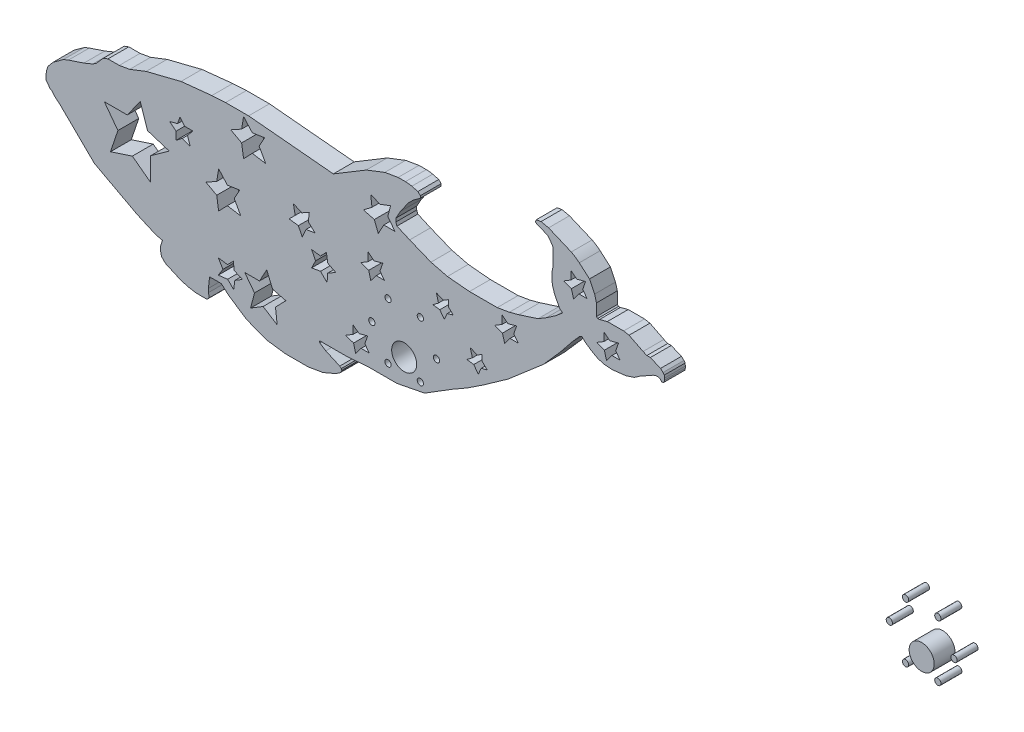
SolidWorks part; units mm, degrees
ref_plane "前视基准面" through (0, 0, 0) normal (0, 0, 1) x (1, 0, 0)
ref_plane "上视基准面" through (0, 0, 0) normal (0, 1, 0) x (1, 0, 0)
ref_plane "右视基准面" through (0, 0, 0) normal (1, 0, 0) x (0, 0, -1)
sketch "草图1" plane through (0, 0, 0) normal (0, 0, 1) x (1, 0, 0)
  line L0 (83.5762, -152.1775) -> (616.9095, -152.1775) construction
  line L5 (70.5984, -139.437) -> (603.9317, -139.437) construction
  line L6 (-33.4107, 54.8311) -> (-37.6598, 53.0815)
  line L7 (-37.6598, 53.0815) -> (-42.0588, 51.6318)
  line L8 (-42.0588, 51.6318) -> (-45.0467, 50.6472)
  line L9 (-45.0467, 50.6472) -> (-47.4328, 49.6647)
  line L10 (-47.4328, 49.6647) -> (-49.7572, 47.9826)
  line L11 (-49.7572, 47.9826) -> (-51.1926, 46.9439)
  line L12 (-51.1926, 46.9439) -> (-52.408, 46.0643)
  line L13 (-52.408, 46.0643) -> (-53.6631, 44.5741)
  line L14 (-53.6631, 44.5741) -> (-54.8675, 43.1441)
  line L15 (-54.8675, 43.1441) -> (-55.4833, 41.2781)
  line L20 (-55.8277, 37.0689) -> (-55.0465, 35.9894)
  line L21 (-55.0465, 35.9894) -> (-53.6631, 34.0778)
  line L22 (-53.6631, 34.0778) -> (-53.0356, 34.0778)
  line L23 (-53.0356, 34.0778) -> (-51.8003, 32.3709)
  line L24 (-51.8003, 32.3709) -> (-49.7572, 30.6501)
  line L25 (-49.7572, 30.6501) -> (-48.9668, 29.9844)
  line L26 (-48.9668, 29.9844) -> (-40.5644, 21.7347)
  line L27 (-40.5644, 21.7347) -> (-32.6032, 13.9182)
  line L28 (-32.6032, 13.9182) -> (-27.2854, 11.0838)
  line L29 (-27.2854, 11.0838) -> (-23.2682, 8.9427)
  line L30 (-23.2682, 8.9427) -> (-20.2984, 7.3598)
  line L31 (-20.2984, 7.3598) -> (-16.8647, 5.5296)
  line L32 (-16.8647, 5.5296) -> (-12.13, 3.0061)
  line L33 (-12.13, 3.0061) -> (-7.8019, 1.089)
  line L34 (-7.8019, 1.089) -> (-4.074, -0.5623)
  line L35 (-4.074, -0.5623) -> (-0.6643, -1.6353)
  line L36 (-0.6643, -1.6353) -> (0, -1.6353)
  line L37 (0, -1.6353) -> (-0.9026, -4.5034)
  line L38 (-0.9026, -4.5034) -> (-0.9026, -6.541)
  line L57 (22.4574, -6.541) -> (22.4574, -5.5222)
  line L58 (22.4574, -5.5222) -> (26.7724, -5.5222)
  line L59 (26.7724, -5.5222) -> (28.1702, -5.5222)
  line L60 (28.1702, -5.5222) -> (31.7282, -8.649)
  line L61 (31.7282, -8.649) -> (35.5739, -11.2197)
  line L62 (35.5739, -11.2197) -> (39.8011, -14.0455)
  line L63 (39.8011, -14.0455) -> (44.1213, -15.9591)
  line L64 (44.1213, -15.9591) -> (49.9981, -18.0843)
  line L65 (49.9981, -18.0843) -> (54.9833, -18.758)
  line L66 (54.9833, -18.758) -> (58.9433, -19.2932)
  line L67 (58.9433, -19.2932) -> (64.9003, -19.2932)
  line L68 (64.9003, -19.2932) -> (69.8738, -19.2932)
  line L69 (69.8738, -19.2932) -> (76.9587, -18.0843)
  line L70 (76.9587, -18.0843) -> (81.9059, -15.9591)
  line L71 (81.9059, -15.9591) -> (84.7973, -14.43)
  line L72 (84.7973, -14.43) -> (85.7047, -13.3974)
  line L73 (85.7047, -13.3974) -> (85.9813, -12.6326)
  line L74 (85.9813, -12.6326) -> (85.7274, -12.0415)
  line L75 (85.7274, -12.0415) -> (84.9774, -11.3825)
  line L76 (84.9774, -11.3825) -> (83.1426, -10.5697)
  line L77 (83.1426, -10.5697) -> (78.2926, -8.4214)
  line L78 (78.2926, -8.4214) -> (75.9827, -6.8773)
  line L79 (75.9827, -6.8773) -> (75.4796, -6.541)
  line L80 (75.4796, -6.541) -> (75.2607, -6.0316)
  line L81 (75.2607, -6.0316) -> (75.2607, -5.6862)
  line L82 (75.2607, -5.6862) -> (77.4695, -5.6862)
  line L83 (77.4695, -5.6862) -> (88.6645, -5.6862)
  line L84 (88.6645, -5.6862) -> (98.3767, -4.8754)
  line L87 (125.6251, -2.2946) -> (128.8782, -0.2757)
  line L88 (128.8782, -0.2757) -> (139.0992, 6.0678)
  line L89 (139.0992, 6.0678) -> (145.991, 10.0132)
  line L90 (145.991, 10.0132) -> (154.1306, 15.4027)
  line L91 (154.1306, 15.4027) -> (165.6842, 23.5709)
  line L92 (165.6842, 23.5709) -> (174.7548, 31.3817)
  line L93 (174.7548, 31.3817) -> (182.7359, 38.2543)
  line L94 (182.7359, 38.2543) -> (190.688, 47.3033)
  line L95 (190.688, 47.3033) -> (196.4524, 54.437)
  line L96 (196.4524, 54.437) -> (199.7963, 58.2421)
  line L97 (199.7963, 58.2421) -> (200.6278, 58.8201)
  line L98 (200.6278, 58.8201) -> (201.3219, 58.8201)
  line L99 (201.3219, 58.8201) -> (201.7237, 58.2421)
  line L100 (201.7237, 58.2421) -> (202.973, 57.1442)
  line L101 (202.973, 57.1442) -> (205.3877, 55.4732)
  line L102 (205.3877, 55.4732) -> (208.6354, 53.6139)
  line L103 (208.6354, 53.6139) -> (211.8335, 52.7462)
  line L104 (211.8335, 52.7462) -> (215.4778, 52.4239)
  line L105 (215.4778, 52.4239) -> (222.1425, 53.18)
  line L106 (222.1425, 53.18) -> (226.2551, 54.5436)
  line L107 (226.2551, 54.5436) -> (228.7947, 56.3087)
  line L108 (228.7947, 56.3087) -> (233.2216, 58.8201)
  line L109 (233.2216, 58.8201) -> (235.1797, 59.9309)
  line L110 (235.1797, 59.9309) -> (236.6838, 60.4296)
  line L111 (236.6838, 60.4296) -> (237.6413, 60.4296)
  line L112 (237.6413, 60.4296) -> (238.7462, 59.9309)
  line L113 (238.7462, 59.9309) -> (239.1322, 59.3755)
  line L114 (239.1322, 59.3755) -> (239.4779, 59.2195)
  line L115 (239.4779, 59.2195) -> (239.8353, 59.2195)
  line L116 (239.8353, 59.2195) -> (240.4593, 59.6532)
  line L117 (240.4593, 59.6532) -> (240.6282, 60.5924)
  line L118 (240.6282, 60.5924) -> (240.6282, 61.4324)
  line L119 (240.6282, 61.4324) -> (240.5437, 62.6546)
  line L120 (240.5437, 62.6546) -> (239.9752, 63.4725)
  line L121 (239.9752, 63.4725) -> (238.7462, 64.5403)
  line L122 (238.7462, 64.5403) -> (236.6838, 65.4133)
  line L123 (236.6838, 65.4133) -> (235.1797, 66.05)
  line L124 (235.1797, 66.05) -> (233.8657, 66.6062)
  line L125 (233.8657, 66.6062) -> (232.1914, 66.6062)
  line L126 (232.1914, 66.6062) -> (230.3774, 67.3741)
  line L127 (230.3774, 67.3741) -> (225.9144, 69.6248)
  line L128 (225.9144, 69.6248) -> (223.6572, 70.7632)
  line L129 (223.6572, 70.7632) -> (221.0484, 71.2325)
  line L130 (221.0484, 71.2325) -> (219.2218, 71.2325)
  line L131 (219.2218, 71.2325) -> (213.2492, 71.2325)
  line L132 (213.2492, 71.2325) -> (209.478, 70.194)
  line L133 (209.478, 70.194) -> (208.6354, 70.194)
  line L134 (208.6354, 70.194) -> (208.0377, 70.7133)
  line L135 (208.0377, 70.7133) -> (208.0377, 73.1258)
  line L136 (208.0377, 73.1258) -> (208.0377, 76.3796)
  line L137 (208.0377, 76.3796) -> (207.1546, 79.5865)
  line L138 (207.1546, 79.5865) -> (204.6981, 84.6475)
  line L139 (204.6981, 84.6475) -> (199.7963, 88.906)
  line L140 (195.939, 91.4741) -> (190.688, 93.6969)
  line L141 (190.688, 93.6969) -> (186.8388, 95.3263)
  line L142 (186.8388, 95.3263) -> (185.0851, 96.0686)
  line L143 (185.0851, 96.0686) -> (181.4705, 96.8481)
  line L144 (181.4705, 96.8481) -> (179.1749, 96.4584)
  line L145 (179.1749, 96.4584) -> (178.653, 95.2254)
  line L146 (178.653, 95.2254) -> (179.7411, 94.7648)
  line L147 (179.7411, 94.7648) -> (182.264, 93.6969)
  line L148 (182.264, 93.6969) -> (184.6819, 92.6734)
  line L149 (184.6819, 92.6734) -> (185.9619, 91.1644)
  line L150 (185.9619, 91.1644) -> (187.1532, 89.1995)
  line L151 (187.1532, 89.1995) -> (187.1532, 86.7554)
  line L152 (187.1532, 86.7554) -> (187.1532, 83.0174)
  line L153 (187.1532, 83.0174) -> (187.1532, 80.6692)
  line L154 (187.1532, 80.6692) -> (186.6424, 78.3005)
  line L155 (186.6424, 78.3005) -> (186.6424, 76.3796)
  line L156 (186.6424, 76.3796) -> (186.6424, 75.1921)
  line L157 (186.6424, 75.1921) -> (187.0459, 72.8151)
  line L158 (187.0459, 72.8151) -> (187.8822, 70.194)
  line L159 (187.8822, 70.194) -> (189.2793, 67.3741)
  line L160 (189.2793, 67.3741) -> (190.2507, 65.4133)
  line L161 (190.2507, 65.4133) -> (191.8011, 64.071)
  line L162 (191.8011, 64.071) -> (188.5807, 61.3393)
  line L163 (188.5807, 61.3393) -> (184.0423, 58.2421)
  line L164 (184.0423, 58.2421) -> (179.9948, 55.7882)
  line L165 (179.9948, 55.7882) -> (176.1321, 54.5558)
  line L166 (176.1321, 54.5558) -> (170.8442, 52.8687)
  line L167 (170.8442, 52.8687) -> (166.275, 51.6318)
  line L168 (166.275, 51.6318) -> (162.4428, 50.9811)
  line L169 (162.4428, 50.9811) -> (160.4758, 50.6472)
  line L170 (160.4758, 50.6472) -> (147.1514, 50.6472)
  line L171 (147.1514, 50.6472) -> (136.6018, 51.6318)
  line L172 (136.6018, 51.6318) -> (128.697, 53.6139)
  line L173 (128.697, 53.6139) -> (118.4882, 57.7541)
  line L174 (118.4882, 57.7541) -> (112.413, 60.4296)
  line L175 (112.413, 60.4296) -> (111.8604, 61.8521)
  line L176 (111.8604, 61.8521) -> (111.8604, 63.4725)
  line L177 (111.8604, 63.4725) -> (114.0757, 67.3741)
  line L178 (114.0757, 67.3741) -> (117.8675, 72.8151)
  line L179 (117.8675, 72.8151) -> (120.3102, 75.1921)
  line L180 (120.3102, 75.1921) -> (122.6457, 76.8963)
  line L181 (122.6457, 76.8963) -> (123.5926, 77.5873)
  line L182 (123.5926, 77.5873) -> (123.5926, 78.6479)
  line L183 (123.5926, 78.6479) -> (122.4473, 79.8248)
  line L184 (122.4473, 79.8248) -> (119.527, 80.5571)
  line L185 (116.4835, 80.9328) -> (112.968, 80.9328)
  line L186 (112.968, 80.9328) -> (106.5857, 79.8248)
  line L187 (106.5857, 79.8248) -> (97.718, 76.3796)
  line L188 (97.718, 76.3796) -> (91.8005, 72.8151)
  line L189 (91.8005, 72.8151) -> (86.9276, 69.8798)
  line L190 (86.9276, 69.8798) -> (83.1426, 67.5998)
  line L191 (83.1426, 67.5998) -> (81.9059, 66.8548)
  line L192 (81.9059, 66.8548) -> (61.7102, 68.7398)
  line L193 (61.7102, 68.7398) -> (49.496, 69.8798)
  line L194 (49.496, 69.8798) -> (41.2874, 70.6459)
  line L195 (41.2874, 70.6459) -> (35.0487, 70.6459)
  line L196 (35.0487, 70.6459) -> (30.2431, 70.6459)
  line L197 (30.2431, 70.6459) -> (23.667, 70.2629)
  line L198 (23.667, 70.2629) -> (8.9087, 68.7398)
  line L199 (8.9087, 68.7398) -> (-7.8019, 64.5403)
  line L200 (-7.8019, 64.5403) -> (-15.705, 61.4699)
  line L201 (-15.705, 61.4699) -> (-20.7029, 60.5924)
  line L202 (-20.7029, 60.5924) -> (-24.374, 60.5924)
  line L203 (-24.374, 60.5924) -> (-26.1248, 60.5924)
  line L204 (-26.1248, 60.5924) -> (-28.3735, 59.7188)
  line L205 (-28.3735, 59.7188) -> (-30.1347, 57.7541)
  line L206 (-30.1347, 57.7541) -> (-31.7347, 55.9692)
  line L207 (-31.7347, 55.9692) -> (-33.4107, 54.8311)
  line L208 (142.6379, -266.3219) -> (825.3045, -266.3219) construction
  line L209 (66.7963, 43.1441) -> (70.4146, 45.1685)
  line L210 (70.4146, 45.1685) -> (69.8738, 41.0482)
  line L211 (69.8738, 41.0482) -> (73.1335, 37.9737)
  line L212 (73.1335, 37.9737) -> (68.8251, 37.2626)
  line L213 (68.8251, 37.2626) -> (67.0264, 33.226)
  line L214 (67.0264, 33.226) -> (65.1231, 36.9943)
  line L215 (65.1231, 36.9943) -> (60.6892, 37.5763)
  line L216 (60.6892, 37.5763) -> (63.6172, 40.4835)
  line L217 (63.6172, 40.4835) -> (62.7388, 44.9593)
  line L218 (62.7388, 44.9593) -> (66.7963, 43.1441)
  line L219 (-10.6553, 50.6472) -> (-16.8647, 41.9395)
  line L220 (-16.8647, 41.9395) -> (-27.8682, 41.9395)
  line L221 (-27.8682, 41.9395) -> (-21.3687, 33.226)
  line L222 (-21.3687, 33.226) -> (-24.9339, 22.6357)
  line L223 (-24.9339, 22.6357) -> (-14.4384, 26.0662)
  line L224 (-14.4384, 26.0662) -> (-5.624, 19.4843)
  line L225 (-5.624, 19.4843) -> (-5.624, 30.6501)
  line L226 (-5.624, 30.6501) -> (3.21, 36.9943)
  line L227 (3.21, 36.9943) -> (-7.1957, 40.2986)
  line L228 (-7.1957, 40.2986) -> (-10.6553, 50.6472)
  line L239 (78.5852, 32.6805) -> (75.7678, 29.6934)
  line L240 (75.7678, 29.6934) -> (71.5037, 30.2531)
  line L241 (71.5037, 30.2531) -> (73.3981, 26.5024)
  line L242 (73.3981, 26.5024) -> (71.5037, 22.6357)
  line L243 (71.5037, 22.6357) -> (75.7678, 23.3633)
  line L244 (75.7678, 23.3633) -> (78.9066, 20.202)
  line L245 (78.9066, 20.202) -> (79.2299, 24.351)
  line L246 (79.2299, 24.351) -> (83.1426, 26.5399)
  line L247 (83.1426, 26.5399) -> (79.2299, 28.4569)
  line L248 (79.2299, 28.4569) -> (78.5852, 32.6805)
  line L249 (38.8838, 69.1883) -> (37.946, 63.4725)
  line L250 (37.946, 63.4725) -> (32.752, 60.5924)
  line L251 (32.752, 60.5924) -> (37.946, 57.7541)
  line L252 (37.946, 57.7541) -> (38.8806, 51.6318)
  line L253 (38.8806, 51.6318) -> (43.0679, 55.9692)
  line L254 (43.0679, 55.9692) -> (49.496, 54.9145)
  line L255 (49.496, 54.9145) -> (46.3476, 60.5924)
  line L256 (46.3476, 60.5924) -> (48.982, 65.4133)
  line L257 (48.982, 65.4133) -> (43.0679, 64.5105)
  line L258 (43.0679, 64.5105) -> (38.8838, 69.1883)
  line L259 (8.4234, 53.8005) -> (10.5741, 50.9811)
  line L260 (10.5741, 50.9811) -> (14.503, 50.9811)
  line L261 (14.503, 50.9811) -> (12.0042, 47.7509)
  line L262 (12.0042, 47.7509) -> (13.2536, 44.0449)
  line L263 (13.2536, 44.0449) -> (9.4987, 45.3925)
  line L264 (9.4987, 45.3925) -> (6.5513, 43.1441)
  line L265 (6.5513, 43.1441) -> (6.5513, 46.9439)
  line L266 (6.5513, 46.9439) -> (3.4201, 49.366)
  line L267 (3.4201, 49.366) -> (7.2312, 50.3901)
  line L268 (7.2312, 50.3901) -> (8.4234, 53.8005)
  line L269 (91.3541, 8.9427) -> (94.2268, 6.7205)
  line L270 (94.2268, 6.7205) -> (98.3767, 7.8356)
  line L271 (98.3767, 7.8356) -> (97.0015, 3.9016)
  line L272 (97.0015, 3.9016) -> (99.1471, 1.089)
  line L273 (99.1471, 1.089) -> (95.2383, 1.089)
  line L274 (95.2383, 1.089) -> (92.6208, -2.2946)
  line L275 (92.6208, -2.2946) -> (91.7117, 1.089)
  line L276 (91.7117, 1.089) -> (91.6028, 1.494)
  line L277 (91.6028, 1.494) -> (87.8302, 2.8128)
  line L278 (87.8302, 2.8128) -> (91.3541, 4.952)
  line L279 (91.3541, 4.952) -> (91.3541, 8.9427)
  line L280 (99.8281, 67.3741) -> (104.2265, 65.4133)
  line L281 (104.2265, 65.4133) -> (109.3417, 67.3741)
  line L282 (109.3417, 67.3741) -> (108.0186, 62.2542)
  line L283 (108.0186, 62.2542) -> (111.4514, 57.7541)
  line L284 (111.4514, 57.7541) -> (106.1158, 57.7541)
  line L285 (106.1158, 57.7541) -> (103.4365, 52.8687)
  line L286 (103.4365, 52.8687) -> (101.5638, 57.7541)
  line L287 (101.5638, 57.7541) -> (96.3017, 59.114)
  line L288 (96.3017, 59.114) -> (100.4183, 62.2542)
  line L289 (100.4183, 62.2542) -> (99.8281, 67.3741)
  line L310 (49.9981, 11.0838) -> (46.5028, 4.7104)
  line L311 (46.5028, 4.7104) -> (39.4303, 4.7104)
  line L312 (39.4303, 4.7104) -> (44.1213, -1.4392)
  line L313 (44.1213, -1.4392) -> (42.2581, -8.649)
  line L314 (42.2581, -8.649) -> (48.2504, -5.0114)
  line L315 (48.2504, -5.0114) -> (54.9833, -9.2652)
  line L316 (54.9833, -9.2652) -> (54.1798, -2.2946)
  line L317 (54.1798, -2.2946) -> (59.131, 2.8128)
  line L318 (59.131, 2.8128) -> (52.7682, 4.4571)
  line L319 (52.7682, 4.4571) -> (49.9981, 11.0838)
  line L320 (33.9476, 6.6705) -> (31.2237, 3.8607)
  line L321 (31.2237, 3.8607) -> (26.7724, 4.4596)
  line L322 (26.7724, 4.4596) -> (28.9981, 0.7932)
  line L323 (28.9981, 0.7932) -> (26.7724, -2.7296)
  line L324 (26.7724, -2.7296) -> (31.2237, -2.2165)
  line L325 (31.2237, -2.2165) -> (34.1405, -5.0441)
  line L326 (34.1405, -5.0441) -> (34.6889, -0.9682)
  line L327 (34.6889, -0.9682) -> (38.3288, 1.2413)
  line L328 (38.3288, 1.2413) -> (34.4147, 2.9862)
  line L329 (34.4147, 2.9862) -> (33.9476, 6.6705)
  line L330 (98.3767, -4.8754) -> (112.413, -4.8754)
  line L331 (112.413, -4.8754) -> (125.6251, -2.2946)
  line L332 (195.7788, 83.7389) -> (198.6514, 81.5168)
  line L333 (198.6514, 81.5168) -> (202.8014, 82.6319)
  line L334 (202.8014, 82.6319) -> (201.4262, 78.6978)
  line L335 (201.4262, 78.6978) -> (203.5717, 75.8852)
  line L336 (203.5717, 75.8852) -> (199.6629, 75.8852)
  line L337 (199.6629, 75.8852) -> (197.0455, 72.5016)
  line L338 (197.0455, 72.5016) -> (196.1363, 75.8852)
  line L339 (196.1363, 75.8852) -> (196.0275, 76.2903)
  line L340 (196.0275, 76.2903) -> (192.2548, 77.6091)
  line L341 (192.2548, 77.6091) -> (195.7788, 79.7482)
  line L342 (195.7788, 79.7482) -> (195.7788, 83.7389)
  line L343 (162.7419, 48.7713) -> (165.6145, 46.5491)
  line L344 (165.6145, 46.5491) -> (169.7645, 47.6643)
  line L345 (169.7645, 47.6643) -> (168.3893, 43.7302)
  line L346 (168.3893, 43.7302) -> (170.5348, 40.9176)
  line L347 (170.5348, 40.9176) -> (166.626, 40.9176)
  line L348 (166.626, 40.9176) -> (164.0086, 37.534)
  line L349 (164.0086, 37.534) -> (163.0994, 40.9176)
  line L350 (163.0994, 40.9176) -> (162.9906, 41.3226)
  line L351 (162.9906, 41.3226) -> (159.2179, 42.6414)
  line L352 (159.2179, 42.6414) -> (162.7419, 44.7806)
  line L353 (162.7419, 44.7806) -> (162.7419, 48.7713)
  line L354 (98.5988, 42.7646) -> (101.4714, 40.5424)
  line L355 (101.4714, 40.5424) -> (105.6214, 41.6575)
  line L356 (105.6214, 41.6575) -> (104.2462, 37.7235)
  line L357 (104.2462, 37.7235) -> (106.3917, 34.9109)
  line L358 (106.3917, 34.9109) -> (102.4829, 34.9109)
  line L359 (102.4829, 34.9109) -> (99.8655, 31.5273)
  line L360 (99.8655, 31.5273) -> (98.9563, 34.9109)
  line L361 (98.9563, 34.9109) -> (98.8475, 35.3159)
  line L362 (98.8475, 35.3159) -> (95.0748, 36.6347)
  line L363 (95.0748, 36.6347) -> (98.5988, 38.7739)
  line L364 (98.5988, 38.7739) -> (98.5988, 42.7646)
  line L375 (136.9988, 42.2088) -> (134.5919, 40.7478)
  line L376 (134.5919, 40.7478) -> (131.2852, 42.2219)
  line L377 (131.2852, 42.2219) -> (132.3012, 38.4406)
  line L378 (132.3012, 38.4406) -> (129.659, 36.425)
  line L379 (129.659, 36.425) -> (132.9386, 35.9837)
  line L380 (132.9386, 35.9837) -> (135.1416, 33.0957)
  line L381 (135.1416, 33.0957) -> (136.5274, 36.2044)
  line L382 (136.5274, 36.2044) -> (139.3906, 36.9737)
  line L383 (139.3906, 36.9737) -> (136.9988, 39.2924)
  line L384 (136.9988, 39.2924) -> (136.9988, 42.2088)
  line L385 (153.2609, 27.5965) -> (150.854, 26.1354)
  line L386 (150.854, 26.1354) -> (147.5473, 27.6096)
  line L387 (147.5473, 27.6096) -> (148.5633, 23.8283)
  line L388 (148.5633, 23.8283) -> (145.9211, 21.8127)
  line L389 (145.9211, 21.8127) -> (149.2007, 21.3714)
  line L390 (149.2007, 21.3714) -> (151.4037, 18.4834)
  line L391 (151.4037, 18.4834) -> (152.7895, 21.592)
  line L392 (152.7895, 21.592) -> (155.6527, 22.3614)
  line L393 (155.6527, 22.3614) -> (153.2609, 24.68)
  line L394 (153.2609, 24.68) -> (153.2609, 27.5965)
  line L408 (-55.8277, 37.2583) -> (-55.8277, 37.0689)
  line L409 (-55.4833, 41.2781) -> (-55.8277, 39.2924)
  line L410 (-55.8277, 39.2924) -> (-55.8277, 37.2583)
  line L411 (-0.9026, -6.541) -> (-0.4513, -8.649)
  line L412 (-0.4513, -8.649) -> (1.505, -10.5697)
  line L413 (1.505, -10.5697) -> (4.8277, -12.0415)
  line L414 (4.8277, -12.0415) -> (8.4234, -13.6343)
  line L415 (8.4234, -13.6343) -> (12.0042, -14.7611)
  line L416 (12.0042, -14.7611) -> (16.1903, -15.4725)
  line L417 (16.1903, -15.4725) -> (19.7552, -15.4725)
  line L420 (22.4574, -14.2849) -> (22.0436, -12.3518)
  line L421 (22.0436, -12.3518) -> (22.0436, -10.5697)
  line L422 (22.0436, -10.5697) -> (22.4574, -6.541)
  line L423 (19.7552, -15.4725) -> (21.3666, -15.4725)
  line L424 (21.3666, -15.4725) -> (22.4574, -14.2849)
  line L425 (26.9329, 41.4879) -> (25.9951, 35.7721)
  line L426 (25.9951, 35.7721) -> (20.8011, 32.892)
  line L427 (20.8011, 32.892) -> (25.9951, 30.0537)
  line L428 (25.9951, 30.0537) -> (26.9296, 23.9314)
  line L429 (26.9296, 23.9314) -> (31.1169, 28.2687)
  line L430 (31.1169, 28.2687) -> (37.5451, 27.214)
  line L431 (37.5451, 27.214) -> (34.3966, 32.892)
  line L432 (34.3966, 32.892) -> (37.031, 37.7128)
  line L433 (37.031, 37.7128) -> (31.1169, 36.8101)
  line L434 (31.1169, 36.8101) -> (26.9329, 41.4879)
  line L445 (211.5937, 66.0958) -> (214.4663, 63.8737)
  line L446 (214.4663, 63.8737) -> (218.6163, 64.9888)
  line L447 (218.6163, 64.9888) -> (217.2411, 61.0547)
  line L448 (217.2411, 61.0547) -> (219.3866, 58.2421)
  line L449 (219.3866, 58.2421) -> (215.4778, 58.2421)
  line L450 (215.4778, 58.2421) -> (212.8604, 54.8585)
  line L451 (212.8604, 54.8585) -> (211.9512, 58.2421)
  line L452 (211.9512, 58.2421) -> (211.8424, 58.6471)
  line L453 (211.8424, 58.6471) -> (208.0698, 59.9659)
  line L454 (208.0698, 59.9659) -> (211.5937, 62.1051)
  line L455 (211.5937, 62.1051) -> (211.5937, 66.0958)
  arc A0 (199.7963, 88.906) -> (195.939, 91.4741) centre (187.8822, 75.1921) ccw
  arc A1 (119.527, 80.5571) -> (116.4835, 80.9328) centre (116.4835, 68.4191) ccw
  circle A3 centre (115.8643, 7.7704) radius 6
  circle A5 centre (100.3643, 14.7704) radius 1.5
  circle A6 centre (108.1143, 1.347) radius 1.5
  circle A7 centre (123.6143, 1.347) radius 1.5
  circle A8 centre (131.3643, 14.7704) radius 1.5
  circle A9 centre (123.6143, 28.1938) radius 1.5
  circle A10 centre (108.1143, 28.1938) radius 1.5
  circle A11 centre (363.9271, 7.3493) radius 6
  circle A12 centre (348.4271, 14.3493) radius 1.5
  circle A13 centre (356.1771, 0.9259) radius 1.5
  circle A14 centre (371.6771, 0.9259) radius 1.5
  circle A15 centre (379.4271, 14.3493) radius 1.5
  circle A16 centre (371.6771, 27.7727) radius 1.5
  circle A17 centre (356.1771, 27.7727) radius 1.5
  point P232 (115.8643, 14.7704)
  dimension "D1" = 6
extrude "Boss-Extrude1" add sketch "草图1" along normal blind 10
